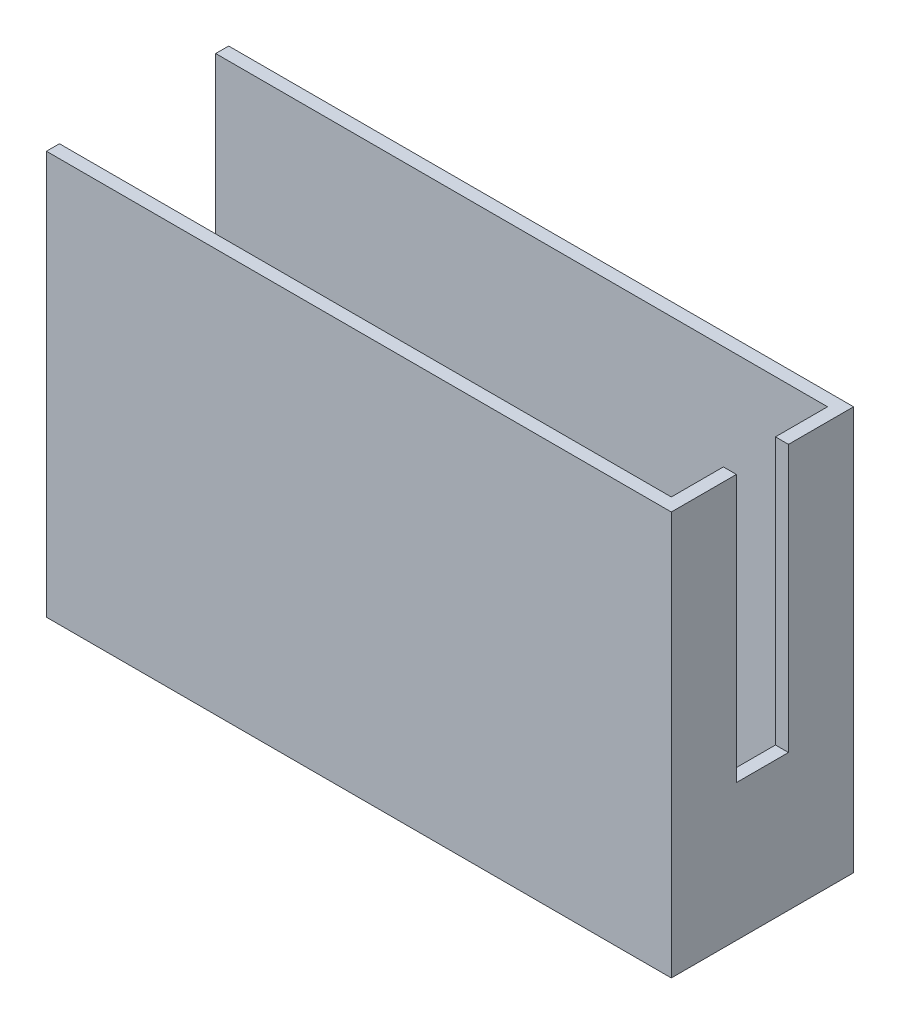
SolidWorks part; units mm, degrees
ref_plane "Front Plane" through (0, 0, 0) normal (0, 0, 1) x (1, 0, 0)
ref_plane "Top Plane" through (0, 0, 0) normal (0, 1, 0) x (1, 0, 0)
ref_plane "Right Plane" through (0, 0, 0) normal (1, 0, 0) x (0, 0, -1)
sketch "Sketch1" plane through (0, 0, 0) normal (0, 1, 0) x (1, 0, 0)
  line L1 (0, 0) -> (96, 0)
  line L2 (0, 0) -> (0, 28)
  line L3 (0, 28) -> (96, 28)
  line L4 (96, 0) -> (96, 28)
extrude "Boss-Extrude1" add sketch "Sketch1" along normal blind 62
sketch "Sketch2" plane through (0, 62, 0) normal (0, 1, 0) x (1, 0, 0)
  line L1 (2, 2) -> (94, 2)
  line L2 (2, 2) -> (2, 26)
  line L3 (2, 26) -> (94, 26)
  line L4 (94, 2) -> (94, 26)
extrude "Cut-Extrude1" cut sketch "Sketch2" against normal blind 60
sketch "Sketch3" plane through (96, 0, 0) normal (1, 0, 0) x (0, 0, -1)
  line L6 (0, 62) -> (28, 62) construction
  line L7 (10, 62) -> (10, 21)
  line L11 (18, 62) -> (18, 21)
  line L12 (18, 21) -> (10, 21)
  line L13 (10, 62) -> (18, 62)
extrude "Cut-Extrude2" cut sketch "Sketch3" against normal blind 12
sketch "Sketch4" plane through (0, 0, 0) normal (-1, 0, 0) x (0, 0, 1)
  line L0 (-26, 62) -> (-2, 62)
  line L2 (-26, 15) -> (-2, 15)
  line L6 (-26, 62) -> (-26, 15)
  line L7 (-2, 62) -> (-2, 15)
  line L8 (-28, 62) -> (0, 62) construction
extrude "Cut-Extrude3" cut sketch "Sketch4" against normal blind 10
